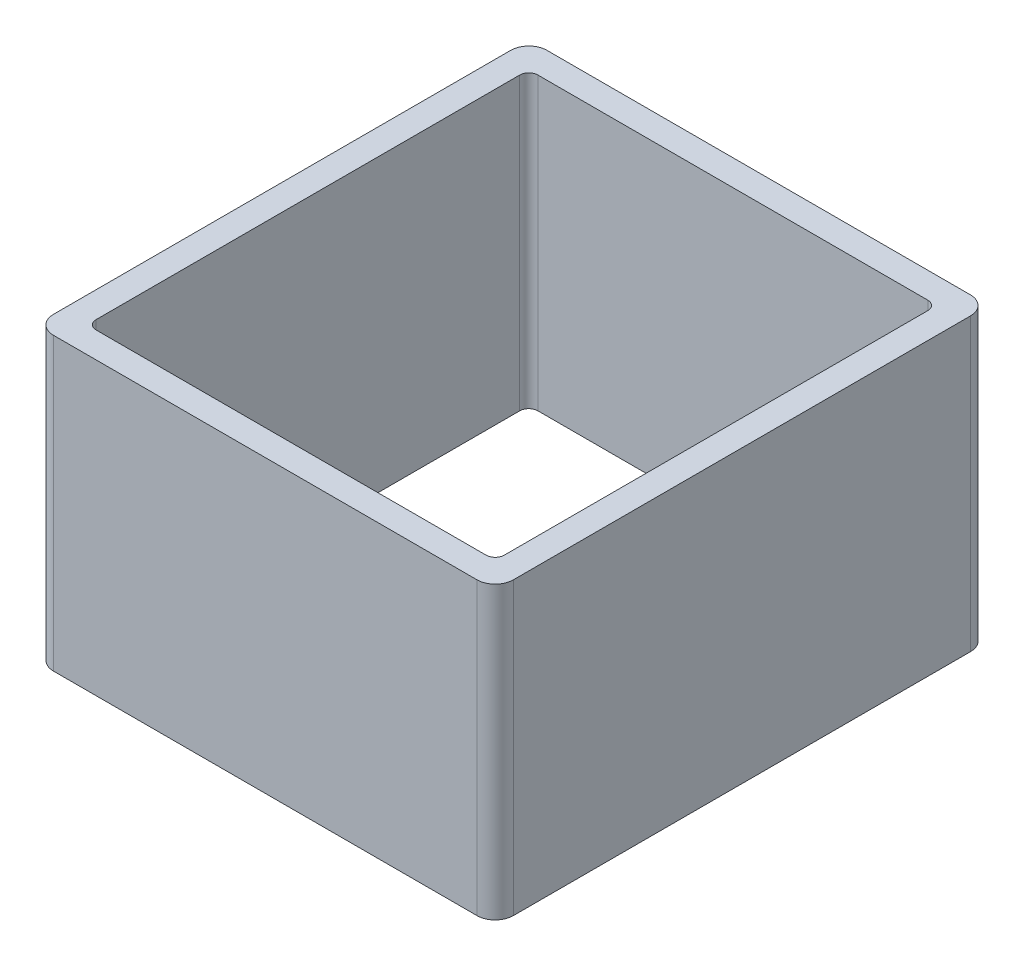
SolidWorks part; units mm, degrees
ref_plane "Front Plane" through (0, 0, 0) normal (0, 0, 1) x (1, 0, 0)
ref_plane "Top Plane" through (0, 0, 0) normal (0, 1, 0) x (1, 0, 0)
ref_plane "Right Plane" through (0, 0, 0) normal (1, 0, 0) x (0, 0, -1)
sketch "Sketch3" plane through (0, 0, 0) normal (0, 1, 0) x (1, 0, 0)
  line L1 (-25.3, -27.15) -> (25.3, -27.15)
  line L2 (-25.3, -27.15) -> (-25.3, 27.15)
  line L3 (-25.3, 27.15) -> (25.3, 27.15)
  line L4 (25.3, -27.15) -> (25.3, 27.15)
  line L5 (-25.3, -27.15) -> (25.3, 27.15) construction
  line L6 (-25.3, 27.15) -> (25.3, -27.15) construction
  line L7 (-22.45, -24.3) -> (22.45, -24.3)
  line L8 (-22.45, -24.3) -> (-22.45, 24.3)
  line L9 (-22.45, 24.3) -> (22.45, 24.3)
  line L10 (22.45, -24.3) -> (22.45, 24.3)
  line L11 (-22.45, -24.3) -> (22.45, 24.3) construction
  line L12 (-22.45, 24.3) -> (22.45, -24.3) construction
  point P0 (0, 0)
  point P6 (0, 0)
  dimension "D1" = 50.6
  dimension "D2" = 54.3
  dimension "D3" = 2.85
  dimension "D4" = 2.85
extrude "Boss-Extrude1" add sketch "Sketch3" along normal blind 32
fillet "Fillet1" radius 2 4 edges at (25.3, 16, -27.15) (25.3, 16, 27.15) (-25.3, 16, 27.15) (-25.3, 16, -27.15)
fillet "Fillet2" radius 1 4 edges at (22.45, 16, -24.3) (22.45, 16, 24.3) (-22.45, 16, 24.3) (-22.45, 16, -24.3)
